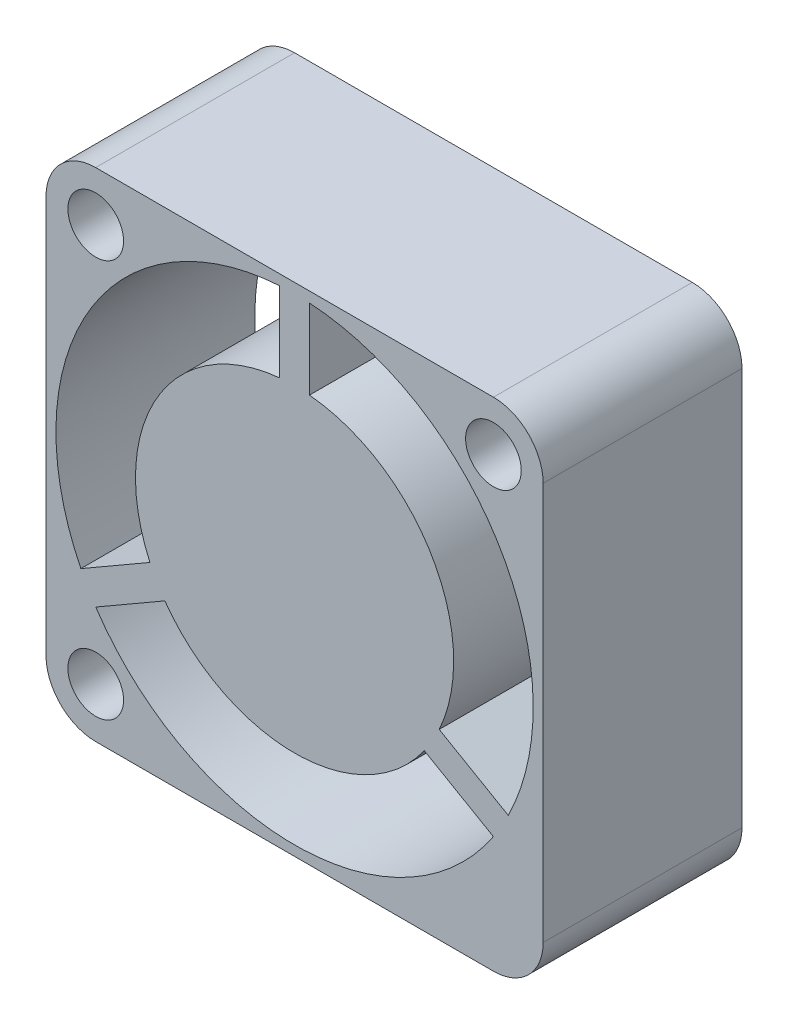
SolidWorks part; units mm, degrees
ref_plane "Front Plane" through (0, 0, 0) normal (0, 0, 1) x (1, 0, 0)
ref_plane "Top Plane" through (0, 0, 0) normal (0, 1, 0) x (1, 0, 0)
ref_plane "Right Plane" through (0, 0, 0) normal (1, 0, 0) x (0, 0, -1)
sketch "Sketch1" plane through (0, 0, 0) normal (0, 0, 1) x (1, 0, 0)
  line L0 (0, 12.5) -> (25, 12.5) construction
  line L1 (0, 0) -> (25, 0)
  line L2 (0, 0) -> (0, 25)
  line L3 (0, 25) -> (25, 25)
  line L4 (25, 0) -> (25, 25)
  line L5 (12.5, 25) -> (12.5, 0) construction
  line L6 (2.5, 22.5) -> (2.5, 25) construction
  line L7 (2.5, 22.5) -> (0, 22.5) construction
  line L8 (0, 2.5) -> (2.5, 2.5) construction
  line L9 (2.5, 2.5) -> (2.5, 0) construction
  line L10 (22.5, 25) -> (22.5, 22.5) construction
  line L11 (22.5, 22.5) -> (25, 22.5) construction
  circle A0 centre (12.5, 12.5) radius 12
  circle A1 centre (2.5, 22.5) radius 1.4
  circle A2 centre (2.5, 2.5) radius 1.4
  circle A3 centre (22.5, 22.5) radius 1.4
  dimension "D2" = 24
  dimension "D3" = 2.8
  dimension "D1" = 25
  dimension "D4" = 20
extrude "Boss-Extrude1" add sketch "Sketch1" along normal blind 10
fillet "Fillet1" radius 2.5 4 edges at (0, 25, 5) (0, 0, 5) (25, 0, 5) (25, 25, 5)
sketch "Sketch2" plane through (0, 0, 10) normal (0, 0, 1) x (1, 0, 0)
  circle A0 centre (12.5, 12.5) radius 8
  dimension "D1" = 16
extrude "Boss-Extrude2" add sketch "Sketch2" against normal up to surface (10 mm away) separate body up to face at (3.9, 2.5, 0)
sketch "Sketch3" plane through (0, 0, 10) normal (0, 0, 1) x (1, 0, 0)
  line L0 (12.5, 24.5) -> (12.5, 12.5) construction
  line L1 (22.5, 25) -> (2.5, 25) construction
  line L2 (11.75, 25) -> (13.25, 25)
  line L3 (11.75, 25) -> (11.75, 20.4648)
  line L4 (11.75, 20.4648) -> (13.25, 20.4648)
  line L5 (13.25, 25) -> (13.25, 20.4648)
  line L6 (23.7003, 6.8995) -> (22.9503, 5.6005)
  line L7 (23.7003, 6.8995) -> (19.7727, 9.1671)
  line L8 (19.7727, 9.1671) -> (19.0227, 7.8681)
  line L9 (22.9503, 5.6005) -> (19.0227, 7.8681)
  line L10 (2.0497, 5.6005) -> (1.2997, 6.8995)
  line L11 (2.0497, 5.6005) -> (5.9773, 7.8681)
  line L12 (5.9773, 7.8681) -> (5.2273, 9.1671)
  line L13 (1.2997, 6.8995) -> (5.2273, 9.1671)
  circle A0 centre (12.5, 12.5) radius 12 construction
  circle A1 centre (12.5, 12.5) radius 8 construction
  point P24 (12.5, 12.5)
  dimension "D1" = 1.5
  dimension "D2" = 3
extrude "Boss-Extrude3" add sketch "Sketch3" against normal up to surface (10 mm away) up to face at (4.5, 12.5, 0)
